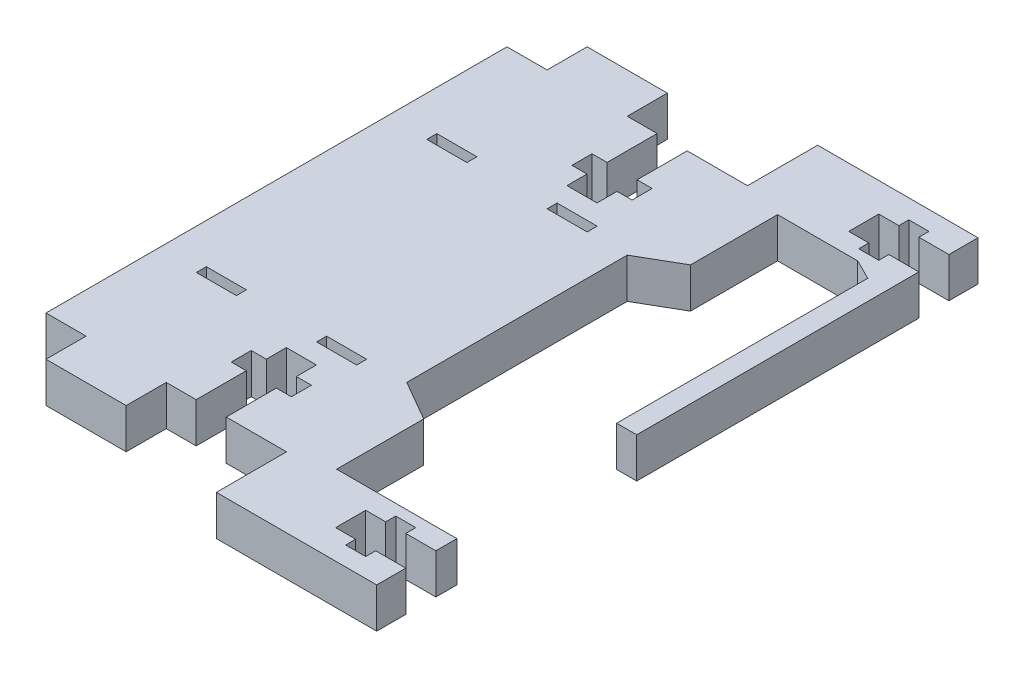
SolidWorks part; units mm, degrees
ref_plane "Front Plane" through (0, 0, 0) normal (0, 0, 1) x (1, 0, 0)
ref_plane "Top Plane" through (0, 0, 0) normal (0, 1, 0) x (1, 0, 0)
ref_plane "Right Plane" through (0, 0, 0) normal (1, 0, 0) x (0, 0, -1)
sketch "Sketch1" plane through (0, 0, 0) normal (0, 1, 0) x (1, 0, 0)
  line L0 (19.05, -19.05) -> (38.1, -19.05)
  line L1 (0, 17.4625) -> (-10.9193, 17.4625) construction
  line L2 (0, 0) -> (0, 34.925)
  line L3 (60.325, 17.4625) -> (68.3008, 17.4625) construction
  line L4 (38.1, 0) -> (38.1, 34.925)
  line L5 (44.45, -17.4625) -> (57.15, -17.4625)
  line L6 (38.1, 0) -> (38.1, 34.925)
  line L7 (44.45, 52.3875) -> (57.15, 52.3875)
  line L8 (60.325, -15.875) -> (60.325, 50.8)
  line L9 (38.1, -30.1625) -> (66.675, -30.1625)
  line L10 (19.05, 53.975) -> (38.1, 53.975)
  line L11 (38.1, 65.0875) -> (66.675, 65.0875)
  line L12 (66.675, -30.1625) -> (66.675, 65.0875)
  line L13 (57.15, 52.3875) -> (60.325, 50.8)
  line L14 (60.325, -15.875) -> (57.15, -17.4625)
  line L15 (38.1, 0) -> (44.45, -3.6662)
  line L16 (44.45, -3.6662) -> (44.45, -17.4625)
  line L17 (38.1, 34.925) -> (44.45, 38.5912)
  line L18 (44.45, 38.5912) -> (44.45, 52.3875)
  line L21 (0, 34.925) -> (0, 53.975)
  line L22 (0, 53.975) -> (6.35, 53.975)
  line L23 (6.35, 53.975) -> (6.35, 60.325)
  line L24 (6.35, 60.325) -> (19.05, 60.325)
  line L25 (0, 0) -> (0, -19.05)
  line L26 (0, -19.05) -> (6.35, -19.05)
  line L27 (19.05, 53.975) -> (19.05, 60.325)
  line L28 (38.1, -30.1625) -> (38.1, -19.05)
  line L29 (6.35, -19.05) -> (6.35, -25.4)
  line L30 (6.35, -25.4) -> (19.05, -25.4)
  line L31 (19.05, -19.05) -> (19.05, -25.4)
  line L33 (38.1, 65.0875) -> (38.1, 53.975)
  dimension "D1" = 34.925
  dimension "D2" = 38.1
  dimension "D3" = 3.175
  dimension "D4" = 1.5875
  dimension "D5" = 69.85
  dimension "D6" = 12.7
  dimension "D7" = 12.7
  dimension "D8" = 6.35
  dimension "D9" = 22.225
  dimension "D10" = 1.5875
  dimension "D11" = 3.175
  dimension "D12" = 19.05
  dimension "D13" = 19.05
  dimension "D14" = 30
  dimension "D15" = 30
  dimension "D17" = 6.35
  dimension "D18" = 0
  dimension "D19" = 6.35
  dimension "D20" = 12.7
  dimension "D21" = 6.35
  dimension "D22" = 6.35
  dimension "D23" = 12.7
  dimension "D24" = 6.35
extrude "Boss-Extrude1" add sketch "Sketch1" along normal blind 6.35 contours L11 L33 L10 L27 L24 L23 L22 L21 L2 L25 L26 L29 L30 L31 L0 L28 L9 L12 L17 L18 L7 L13 L8 L14 L5 L16 L15 L4
sketch "Sketch2" plane through (0, 6.35, 0) normal (0, 1, 0) x (1, 0, 0)
  line L0 (0, -19.05) -> (0, 53.975) construction
  line L1 (6.35, 34.925) -> (12.7, 34.925)
  line L2 (6.35, 34.925) -> (6.35, 36.5125)
  line L3 (6.35, 36.5125) -> (12.7, 36.5125)
  line L4 (12.7, 34.925) -> (12.7, 36.5125)
  line L5 (6.35, 0) -> (12.7, 0)
  line L6 (6.35, 0) -> (6.35, -1.5875)
  line L7 (6.35, -1.5875) -> (12.7, -1.5875)
  line L8 (12.7, 0) -> (12.7, -1.5875)
  line L9 (25.4, 34.925) -> (31.75, 34.925)
  line L10 (25.4, 34.925) -> (25.4, 36.5125)
  line L11 (25.4, 36.5125) -> (31.75, 36.5125)
  line L12 (31.75, 34.925) -> (31.75, 36.5125)
  line L13 (25.4, 0) -> (31.75, 0)
  line L14 (25.4, 0) -> (25.4, -1.5875)
  line L15 (25.4, -1.5875) -> (31.75, -1.5875)
  line L16 (31.75, 0) -> (31.75, -1.5875)
  dimension "D1" = 6.35
  dimension "D2" = 6.35
  dimension "D3" = 12.7
  dimension "D4" = 6.35
  dimension "D5" = 6.35
  dimension "D6" = 6.35
  dimension "D7" = 12.7
  dimension "D8" = 6.35
  dimension "D9" = 1.5875
  dimension "D10" = 1.5875
  dimension "D11" = 1.5875
  dimension "D12" = 1.5875
  dimension "D13" = 0
  dimension "D14" = 0
extrude "Cut-Extrude1" cut sketch "Sketch2" against normal blind 6.35
sketch "Sketch3" plane through (0, 6.35, 0) normal (0, 1, 0) x (1, 0, 0)
  line L0 (19.05, 53.975) -> (38.1, 53.975) construction
  line L1 (23.787, 53.975) -> (28.5495, 53.975)
  line L2 (23.787, 53.975) -> (23.787, 39.6875)
  line L3 (23.787, 39.6875) -> (28.5495, 39.6875)
  line L4 (28.5495, 53.975) -> (28.5495, 39.6875)
  line L5 (66.675, -30.1625) -> (66.675, 65.0875) construction
  line L6 (21.4058, 46.0375) -> (30.9308, 46.0375)
  line L7 (21.4058, 46.0375) -> (21.4058, 42.8625)
  line L8 (21.4058, 42.8625) -> (30.9308, 42.8625)
  line L9 (30.9308, 46.0375) -> (30.9308, 42.8625)
  line L10 (66.675, 60.4838) -> (52.3875, 60.4838)
  line L11 (66.675, 60.4838) -> (66.675, 55.7213)
  line L12 (66.675, 55.7213) -> (52.3875, 55.7213)
  line L13 (52.3875, 60.4838) -> (52.3875, 55.7213)
  line L14 (58.7375, -27.1462) -> (58.7375, -19.2087)
  line L15 (55.5625, 62.0713) -> (58.7375, 62.0713)
  line L16 (55.5625, 62.0713) -> (55.5625, 54.1337)
  line L17 (55.5625, 54.1337) -> (58.7375, 54.1338)
  line L18 (58.7375, 62.0713) -> (58.7375, 54.1338)
  line L19 (38.1, 17.4625) -> (60.325, 17.4625) construction
  line L20 (38.1, 0) -> (38.1, 34.925) construction
  line L21 (60.325, -15.875) -> (60.325, 50.8) construction
  line L22 (52.3875, 58.1025) -> (57.9922, 58.1025) construction
  line L23 (55.5625, -19.2087) -> (58.7375, -19.2087)
  line L24 (55.5625, -27.1462) -> (55.5625, -19.2087)
  line L25 (55.5625, -27.1462) -> (58.7375, -27.1462)
  line L26 (52.3875, -25.5587) -> (52.3875, -20.7962)
  line L27 (66.675, -20.7962) -> (52.3875, -20.7962)
  line L28 (66.675, -25.5587) -> (66.675, -20.7962)
  line L29 (66.675, -25.5587) -> (52.3875, -25.5587)
  line L30 (30.9308, -11.1125) -> (30.9308, -7.9375)
  line L31 (21.4058, -7.9375) -> (30.9308, -7.9375)
  line L32 (21.4058, -11.1125) -> (21.4058, -7.9375)
  line L33 (21.4058, -11.1125) -> (30.9308, -11.1125)
  line L34 (28.5495, -19.05) -> (28.5495, -4.7625)
  line L35 (23.787, -4.7625) -> (28.5495, -4.7625)
  line L36 (23.787, -19.05) -> (23.787, -4.7625)
  line L37 (23.787, -19.05) -> (28.5495, -19.05)
  line M58 (66.675, -30.1625) -> (66.675, 65.0875)
  dimension "D1" = 4.7625
  dimension "D2" = 9.525
  dimension "D3" = 2.3813
  dimension "D4" = 7.9375
  dimension "D5" = 3.175
  dimension "D6" = 3.175
  dimension "D7" = 4.7625
  dimension "D8" = 7.9375
  dimension "D9" = 1.5875
  dimension "D10" = 7.9375
  dimension "D11" = 3.175
  dimension "D12" = 3.175
  dimension "D13" = 40.64
extrude "Cut-Extrude2" cut sketch "Sketch3" against normal blind 6.35 contours L7 L8 L2 L6 | L9 L6 L4 L8 | L16 L10 L13 L12 | L18 L10 L16 L12 | L10 L18 L12 M58 | L26 L27 L28 L29 | L23 L14 L25 L24 | L34 L35 L36 L37 | L33 L30 L31 L32
sketch "Sketch4" plane through (0, 6.35, 0) normal (0, 1, 0) x (1, 0, 0)
  line L0 (38.1, 65.0875) -> (66.675, 65.0875) construction
  line L1 (63.5, 65.0875) -> (100.0194, 65.0875)
  line L2 (63.5, 65.0875) -> (63.5, -30.1625)
  line L3 (63.5, -30.1625) -> (100.0194, -30.1625)
  line L4 (100.0194, 65.0875) -> (100.0194, -30.1625)
  line L5 (60.325, -15.875) -> (60.325, 50.8) construction
  dimension "D1" = 3.175
extrude "Cut-Extrude5" cut sketch "Sketch4" against normal blind 6.35
sketch "Sketch7" plane through (0, 6.35, 0) normal (0, 1, 0) x (1, 0, 0)
  line L0 (44.45, -17.4625) -> (57.15, -17.4625) construction
  line L1 (55.8229, -17.4625) -> (73.9768, -17.4625)
  line L2 (55.8229, -17.4625) -> (55.8229, 11.0252)
  line L3 (55.8229, 11.0252) -> (73.9768, 11.0252)
  line L4 (73.9768, -17.4625) -> (73.9768, 11.0252)
extrude "Cut-Extrude6" cut sketch "Sketch7" against normal blind 6.35
